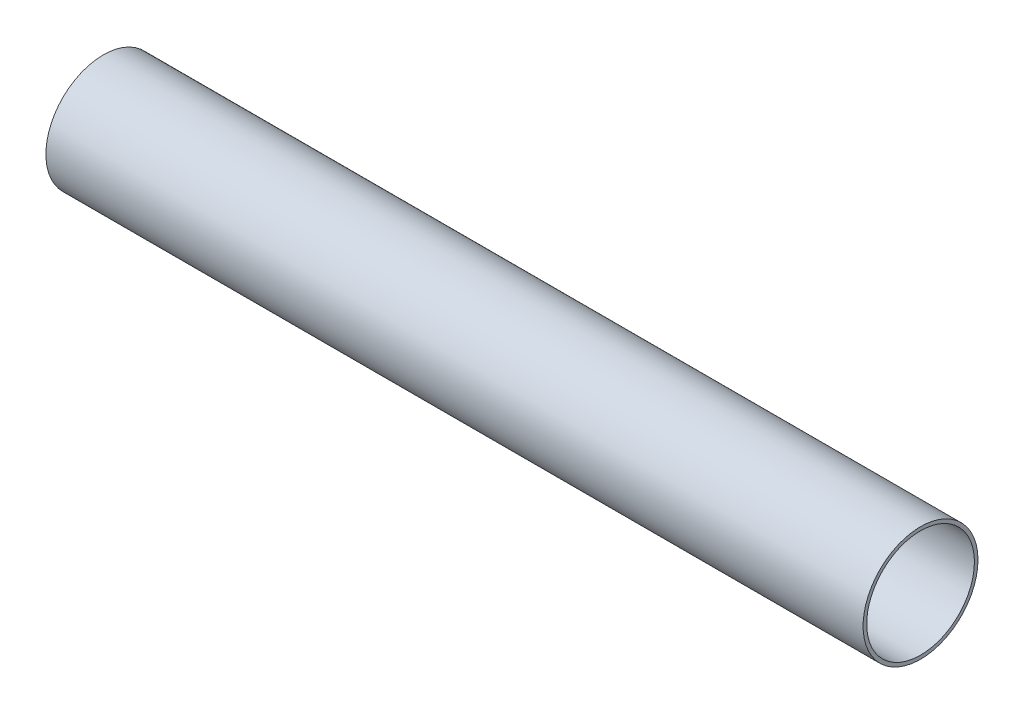
SolidWorks part; units mm, degrees
material "Copper"
ref_plane "Front" through (0, 0, 0) normal (0, 0, 1) x (1, 0, 0)
ref_plane "Top" through (0, 0, 0) normal (0, 1, 0) x (1, 0, 0)
ref_plane "Right" through (0, 0, 0) normal (1, 0, 0) x (0, 0, -1)
sketch "Sketch1" plane through (0, 0, 0) normal (1, 0, 0) x (0, 0, -1)
  circle A0 centre (0, 0) radius 14.2875
  circle A1 centre (0, 0) radius 13.3985
  point P4 (14.2875, 0)
  point P5 (13.3985, 0)
  dimension "OD" = 28.575
  dimension "ID" = 26.797
  dimension "Wall" = 0.889
extrude "Extrude1" add sketch "Sketch1" along normal mid plane 203.2
sketch "Sketch2" plane through (0, 0, 0) normal (0, 0, 1) x (1, 0, 0)
  line L0 (-101.6, 0) -> (101.6, 0) construction
  line L1 (-101.6, 14.2875) -> (-101.6, -14.2875) construction
